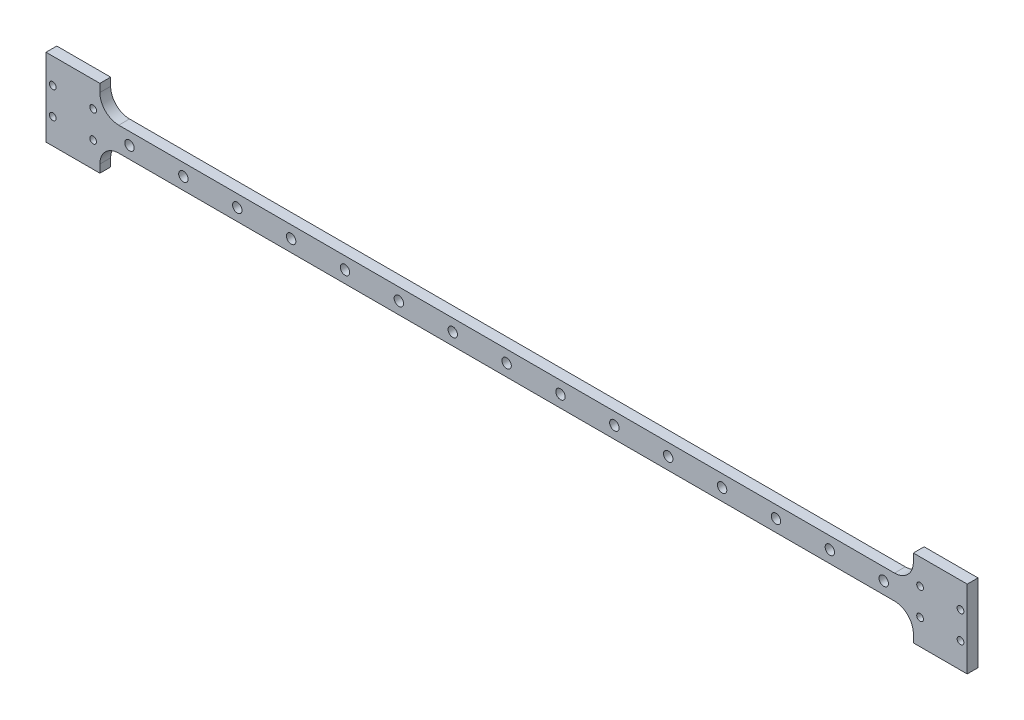
SolidWorks part; units mm, degrees
material "6061 Alloy"
ref_plane "Front Plane" through (0, 0, 0) normal (0, 0, 1) x (1, 0, 0)
ref_plane "Top Plane" through (0, 0, 0) normal (0, 1, 0) x (1, 0, 0)
ref_plane "Right Plane" through (0, 0, 0) normal (1, 0, 0) x (0, 0, -1)
sketch "Sketch1" plane through (0, 0, 0) normal (0, 0, 1) x (1, 0, 0)
  line L0 (-9.79, 14.45) -> (8.7959, 14.45) construction
  line L1 (9.79, -14.45) -> (-8.7959, -14.45) construction
  line L2 (-10, -9.45) -> (-10, 9.45) construction
  line L3 (10, 9.45) -> (10, -9.45) construction
  line L4 (-10, 14.45) -> (8.7959, 14.45)
  line L5 (9.79, -14.45) -> (-8.7959, -14.45)
  line L6 (-10, -9.45) -> (-10, 9.45)
  line L7 (10, 14.45) -> (10, 4.5)
  line L8 (312, -9.45) -> (312, 9.45) construction
  line L9 (312.21, 14.45) -> (330.7959, 14.45) construction
  line L10 (332, 9.45) -> (332, -9.45) construction
  line L11 (331.79, -14.45) -> (313.2041, -14.45) construction
  line L12 (312, -14.45) -> (312, -4.5)
  line L13 (312.21, 14.45) -> (330.7959, 14.45)
  line L14 (332, 14.45) -> (332, -14.45)
  line L15 (331.79, -14.45) -> (313.2041, -14.45)
  line L16 (-10, 9.45) -> (-10, 14.45)
  line L17 (-10, -9.45) -> (-10, -14.45)
  line L18 (8.7959, 14.45) -> (10, 14.45)
  line L20 (9.79, -14.45) -> (10, -14.45)
  line L21 (312.21, 14.45) -> (312, 14.45)
  line L22 (313.2041, -14.45) -> (312, -14.45)
  line L23 (331.79, -14.45) -> (332, -14.45)
  line L24 (330.7959, 14.45) -> (332, 14.45)
  line L25 (11, 4.5) -> (311, 4.5) construction
  line L26 (10, 4.5) -> (312, 4.5)
  line L27 (311, -4.5) -> (11, -4.5) construction
  line L28 (312, -4.5) -> (10, -4.5)
  line L29 (10, -4.5) -> (10, -14.45)
  line L30 (312, 4.5) -> (312, 14.45)
  line L31 (-10, -9.45) -> (-10, -14.45)
  line L32 (-10, -14.45) -> (-8.7959, -14.45)
  arc A0 (22.05, -1.4) -> (19.95, -1.4) centre (21, 0) ccw construction
  circle A4 centre (329.5, -5) radius 1.25 construction
  circle A5 centre (314.5, 5) radius 1.25 construction
  circle A6 centre (314.5, -5) radius 1.25 construction
  arc A7 (22.05, -1.4) -> (19.95, -1.4) centre (21, 0) ccw
  arc A8 (19.95, -1.4) -> (22.05, -1.4) centre (21, 0) ccw
  arc A9 (42.05, -1.4) -> (39.95, -1.4) centre (41, 0) ccw
  arc A10 (39.95, -1.4) -> (42.05, -1.4) centre (41, 0) ccw
  circle A11 centre (329.5, -5) radius 1.25
  circle A12 centre (314.5, 5) radius 1.25
  circle A13 centre (314.5, -5) radius 1.25
  circle A14 centre (329.5, 5) radius 1.25 construction
  circle A15 centre (-7.5, -5) radius 1.25 construction
  circle A16 centre (-7.5, 5) radius 1.25 construction
  circle A17 centre (7.5, -5) radius 1.25 construction
  circle A18 centre (7.5, 5) radius 1.25 construction
  circle A19 centre (329.5, 5) radius 1.25
  circle A20 centre (-7.5, -5) radius 1.25
  circle A21 centre (-7.5, 5) radius 1.25
  circle A22 centre (7.5, -5) radius 1.25
  circle A23 centre (7.5, 5) radius 1.25
  arc A24 (62.05, -1.4) -> (59.95, -1.4) centre (61, 0) ccw
  arc A25 (59.95, -1.4) -> (62.05, -1.4) centre (61, 0) ccw
  arc A26 (82.05, -1.4) -> (79.95, -1.4) centre (81, 0) ccw
  arc A27 (79.95, -1.4) -> (82.05, -1.4) centre (81, 0) ccw
  arc A28 (102.05, -1.4) -> (99.95, -1.4) centre (101, 0) ccw
  arc A29 (99.95, -1.4) -> (102.05, -1.4) centre (101, 0) ccw
  arc A30 (122.05, -1.4) -> (119.95, -1.4) centre (121, 0) ccw
  arc A31 (119.95, -1.4) -> (122.05, -1.4) centre (121, 0) ccw
  arc A32 (142.05, -1.4) -> (139.95, -1.4) centre (141, 0) ccw
  arc A33 (139.95, -1.4) -> (142.05, -1.4) centre (141, 0) ccw
  arc A34 (162.05, -1.4) -> (159.95, -1.4) centre (161, 0) ccw
  arc A35 (159.95, -1.4) -> (162.05, -1.4) centre (161, 0) ccw
  arc A36 (182.05, -1.4) -> (179.95, -1.4) centre (181, 0) ccw
  arc A37 (179.95, -1.4) -> (182.05, -1.4) centre (181, 0) ccw
  arc A38 (202.05, -1.4) -> (199.95, -1.4) centre (201, 0) ccw
  arc A39 (199.95, -1.4) -> (202.05, -1.4) centre (201, 0) ccw
  arc A40 (222.05, -1.4) -> (219.95, -1.4) centre (221, 0) ccw
  arc A41 (219.95, -1.4) -> (222.05, -1.4) centre (221, 0) ccw
  arc A42 (242.05, -1.4) -> (239.95, -1.4) centre (241, 0) ccw
  arc A43 (239.95, -1.4) -> (242.05, -1.4) centre (241, 0) ccw
  arc A44 (262.05, -1.4) -> (259.95, -1.4) centre (261, 0) ccw
  arc A45 (259.95, -1.4) -> (262.05, -1.4) centre (261, 0) ccw
  arc A46 (282.05, -1.4) -> (279.95, -1.4) centre (281, 0) ccw
  arc A47 (279.95, -1.4) -> (282.05, -1.4) centre (281, 0) ccw
  arc A48 (302.05, -1.4) -> (299.95, -1.4) centre (301, 0) ccw
  arc A49 (299.95, -1.4) -> (302.05, -1.4) centre (301, 0) ccw
  dimension "D1" = 15
extrude "Boss-Extrude1" add sketch "Sketch1" along normal blind 4
fillet "Fillet1" radius 7 4 edges at (312, -4.5, 2) (312, 4.5, 2) (10, -4.5, 2) (10, 4.5, 2)
